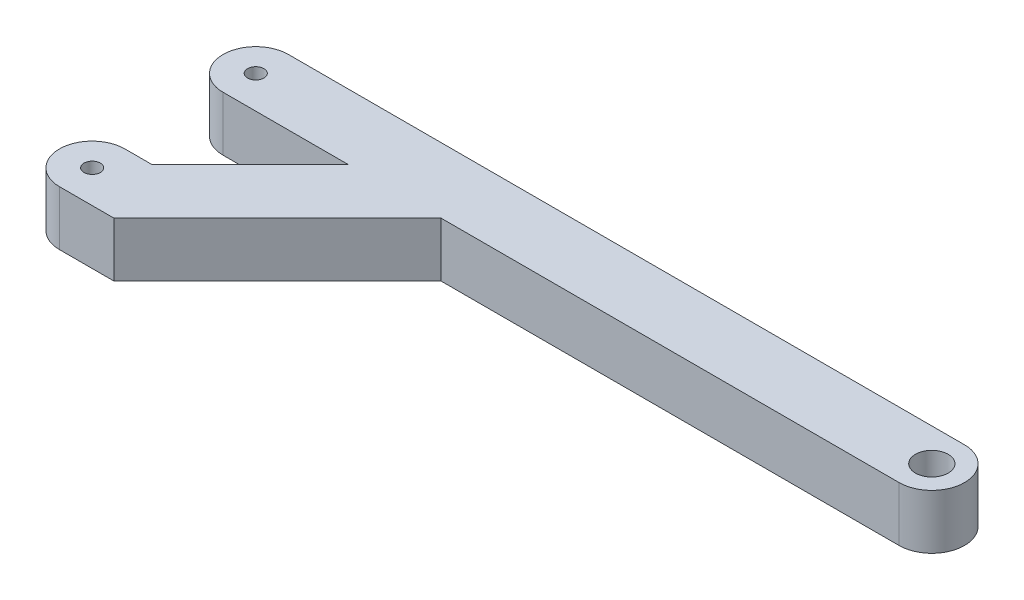
SolidWorks part; units mm, degrees
ref_plane "Front Plane" through (0, 0, 0) normal (0, 0, 1) x (1, 0, 0)
ref_plane "Top Plane" through (0, 0, 0) normal (0, 1, 0) x (1, 0, 0)
ref_plane "Right Plane" through (0, 0, 0) normal (1, 0, 0) x (0, 0, -1)
sketch "Sketch1" plane through (0, 0, 0) normal (0, 1, 0) x (1, 0, 0)
  line L0 (0, 0) -> (-124, 0) construction
  line L1 (0, -6) -> (-124, -6)
  line L2 (0, 6) -> (-124, 6)
  arc A0 (0, -6) -> (0, 6) centre (0, 0) ccw
  arc A1 (-124, 6) -> (-124, -6) centre (-124, 0) ccw
  circle A2 centre (0, 0) radius 3
  circle A3 centre (-124, 0) radius 1.5
  point P3 (-62, 0)
  dimension "D2" = 6
  dimension "D3" = 6
  dimension "D4" = 3
  dimension "D1" = 124
extrude "Boss-Extrude1" add sketch "Sketch1" along normal blind 10
sketch "Sketch2" plane through (0, 10, 0) normal (0, 1, 0) x (1, 0, 0)
  line L0 (-124, -36) -> (-114, -36)
  line L1 (-124, -24) -> (-119, -24)
  line L3 (-119, -24) -> (-101, -6)
  line L4 (-124, -6) -> (0, -6) construction
  line L5 (-114, -36) -> (-84, -6)
  line L6 (-84, -6) -> (-101, -6)
  circle A0 centre (-124, -30) radius 1.5
  circle A1 centre (-124, 0) radius 1.5 construction
  circle A2 centre (-124, 0) radius 1.5
  circle A3 centre (-124, -30) radius 6
  dimension "D2" = 12
  dimension "D1" = 30
  dimension "D3" = 5
  dimension "D4" = 10
  dimension "D5" = 135
extrude "Boss-Extrude2" add sketch "Sketch2" against normal up to surface (10 mm away)
